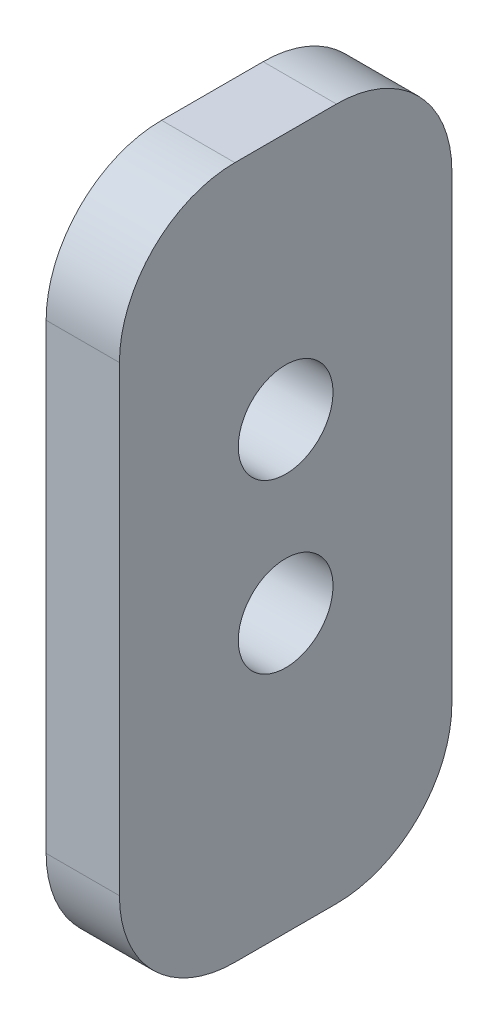
SolidWorks part; units mm, degrees
ref_plane "Front Plane" through (0, 0, 0) normal (0, 0, 1) x (1, 0, 0)
ref_plane "Top Plane" through (0, 0, 0) normal (0, 1, 0) x (1, 0, 0)
ref_plane "Right Plane" through (0, 0, 0) normal (1, 0, 0) x (0, 0, -1)
sketch "Sketch1" plane through (0, 0, 0) normal (1, 0, 0) x (0, 0, -1)
  line L0 (0, -30) -> (0, -6) construction
  line L1 (14.4, -30) -> (-14.4, -30)
  line L2 (14.4, -30) -> (14.4, 30)
  line L3 (14.4, 30) -> (-14.4, 30)
  line L4 (-14.4, -30) -> (-14.4, 30)
  line L5 (14.4, -30) -> (-14.4, 30) construction
  line L6 (14.4, 30) -> (-14.4, -30) construction
  line L7 (0, -6) -> (0, 8.53) construction
  line L8 (0, 8.53) -> (0, 30) construction
  circle A0 centre (0, 8.53) radius 4
  circle A1 centre (0, -6) radius 4
  point P0 (0, 0)
  dimension "D2" = 24
  dimension "D3" = 8
  dimension "D1" = 60
  dimension "D4" = 14.53
  dimension "D5" = 28.8
extrude "Boss-Extrude1" add sketch "Sketch1" along normal blind 6.35 contours A1 | A0 | L4 L1 L2 L3 A1 A0
hole_wizard "5/16 Clearance Hole1" positions "Sketch2" profile "Sketch3" hole size "5/16" standard "ANSI Inch" end condition through all
sketch "Sketch2" plane through (0, 0, 0) normal (-1, 0, 0) x (0, 0, 1)
  point P0 (0, 8.53)
  point P3 (0, -6)
sketch "Sketch3" plane through (0, 8.53, 0) normal (0, 1, 0) x (0, 0, 1)
  line L0 (0, 0) -> (0, 6.35)
  line L1 (0, 6.35) -> (4.1021, 6.35)
  line L2 (4.1021, 6.35) -> (4.1021, 0)
  line L5 (4.1021, 0) -> (0, 0)
  line L11 (0, -6.35) -> (0, 107.95) construction
  dimension "Thru Hole Dia." = 8.2042
  dimension "Thru Hole Depth" = 6.35
fillet "Fillet1" radius 10 4 edges at (3.175, -30, 14.4) (3.175, -30, -14.4) (3.175, 30, 14.4) (3.175, 30, -14.4)
